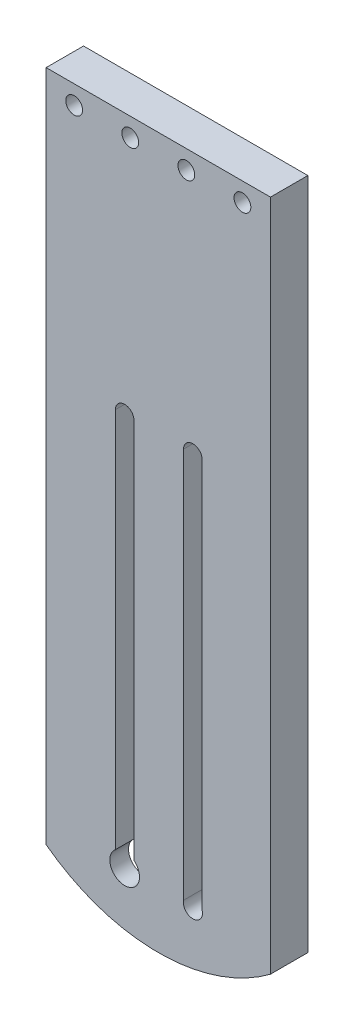
SolidWorks part; units mm, degrees
material "Сплав 2024"
ref_plane "Спереди" through (0, 0, 0) normal (0, 0, 1) x (1, 0, 0)
ref_plane "Сверху" through (0, 0, 0) normal (0, 1, 0) x (1, 0, 0)
ref_plane "Справа" through (0, 0, 0) normal (1, 0, 0) x (0, 0, -1)
sketch "Эскиз1" plane through (0, 0, 0) normal (0, 0, 1) x (1, 0, 0)
  line L0 (31.6276, -80) -> (0, -80) construction
  line L1 (0, 0) -> (60, 0)
  line L2 (0, 0) -> (0, -190)
  line L3 (0, -190) -> (60, -190)
  line L4 (60, 0) -> (60, -60)
  line L5 (30, 0) -> (30, -190) construction
  line L6 (0, -60) -> (-30, -70.9191) construction
  line L7 (-30, -70.9191) -> (-30, -139.0809) construction
  line L8 (-30, -139.0809) -> (0, -150) construction
  line L9 (0, 0) -> (0, -60) construction
  line L10 (0, -150) -> (0, -190) construction
  line L11 (60, -60) -> (60, -150)
  line L15 (60, -150) -> (60, -190)
  line L16 (90, -139.0809) -> (60, -150) construction
  line L17 (90, -70.9191) -> (90, -139.0809) construction
  line L18 (60, -60) -> (90, -70.9191) construction
  dimension "D1" = 40
  dimension "D2" = 190
  dimension "D3" = 80
  dimension "D4" = 60
  dimension "D5" = 60
  dimension "D6" = 90
  dimension "D7" = 110
  dimension "D8" = 110
extrude "Бобышка-Вытянуть1" add sketch "Эскиз1" along normal blind 10
sketch "Эскиз4" plane through (0, 0, 0) normal (0, 0, -1) x (-1, 0, 0)
  line L0 (-30, 0) -> (-30, -190) construction
  line L1 (-40.1, -15) -> (-19.9, -15)
  line L2 (-40.1, -15) -> (-40.1, -64.75)
  line L3 (-40.1, -64.75) -> (-19.9, -64.75)
  line L4 (-19.9, -15) -> (-19.9, -64.75)
  line L5 (-40.1, -15) -> (-19.9, -64.75) construction
  line L6 (-40.1, -64.75) -> (-19.9, -15) construction
  line L7 (0, 0) -> (-60, 0) construction
  point P0 (-30, -39.875)
  dimension "D1" = 20.2
  dimension "D2" = 15
  dimension "D4" = 49.75
hole_wizard "Цековка для винта с внутренним шестигранником M4" positions "Эскиз7" profile "Эскиз8" counterbore size "M4" standard "Ansi Metric"
sketch "Эскиз7" plane through (-14.8427, -41.6551, 0) normal (0, 0, -1) x (-1, 0, 0)
  point P0 (-67.3427, 36.6551)
  point P3 (-52.3427, 36.6551)
  point P6 (-37.3427, 36.6551)
  point P9 (-22.3427, 36.6551)
sketch "Эскиз8" plane through (52.5, -5, 0) normal (1, 0, 0) x (0, 1, 0)
  line L0 (0, 0) -> (0, 11.3509)
  line L1 (0, 11.3509) -> (2.25, 9.999)
  line L2 (2.25, 9.999) -> (2.25, 4)
  line L3 (2.25, 4) -> (4, 4)
  line L4 (4, 4) -> (4, 0)
  line L5 (4, 0) -> (0, 0)
  line L6 (0, 11.3509) -> (-2.25, 9.999) construction
  line L7 (0, -6.35) -> (0, 107.95) construction
  dimension "Диаметр отверстия" = 4.5
  dimension "Глубина отверстия" = 9.999
  dimension "Диаметр цековки" = 8
  dimension "Глубина цековки" = 4
  dimension "Угол заточки сверла" = 118
sketch "Эскиз9" plane through (0, 0, 10) normal (0, 0, -1) x (-1, 0, 0)
  line L0 (-39.25, -190) -> (-39.25, 0) construction
  line L1 (0, -190) -> (-60, -190) construction
  line L2 (-60, 0) -> (0, 0) construction
  line L3 (-21, -190) -> (-21, 0) construction
  line L4 (0, 0) -> (0, -190) construction
  line L5 (-60, -175) -> (0, -175) construction
  line L6 (-60, -190) -> (-60, 0) construction
  dimension "D1" = 18.25
  dimension "D2" = 21
  dimension "D3" = 15
hole_wizard "Отверстие обработанное метчиком 1/4-201" positions "Трехмерный эскиз1" profile "Эскиз10" tap size "1/4-20" standard "Ansi Inch" end condition through all
sketch3d "Трехмерный эскиз1"
  line L0 (60, -175, 10) -> (0, -175, 10) construction
  line L1 (39.25, -190, 10) -> (39.25, 0, 10) construction
  point P0 (39.25, -175, 10)
sketch "Эскиз10" plane through (39.25, -175, 10) normal (1, 0, 0) x (0, -1, 0)
  line L0 (0, 0) -> (0, 10)
  line L1 (0, 10) -> (2.5527, 10)
  line L2 (2.5527, 10) -> (2.5527, 0)
  line L5 (2.5527, 0) -> (0, 0)
  line L11 (0, -6.35) -> (0, 107.95) construction
  dimension "Диаметр резьбы" = 5.1054
  dimension "Глубина проходного сверла" = 10
hole_wizard "Отверстие обработанное метчиком 3/8-161" positions "Трехмерный эскиз2" profile "Эскиз11" tap size "3/8-16" standard "Ansi Inch" end condition through all
sketch3d "Трехмерный эскиз2"
  line L0 (21, -190, 10) -> (21, 0, 10) construction
  line L1 (60, -175, 10) -> (0, -175, 10) construction
  point P0 (21, -175, 10)
sketch "Эскиз11" plane through (21, -175, 10) normal (1, 0, 0) x (0, -1, 0)
  line L0 (0, 0) -> (0, 10)
  line L1 (0, 10) -> (3.9687, 10)
  line L2 (3.9687, 10) -> (3.9687, 0)
  line L5 (3.9687, 0) -> (0, 0)
  line L11 (0, -6.35) -> (0, 107.95) construction
  dimension "Диаметр резьбы" = 7.9375
  dimension "Глубина проходного сверла" = 10
sketch "Эскиз12" plane through (0, 0, 10) normal (0, 0, 1) x (1, 0, 0)
  line L0 (39.25, -175) -> (39.25, -70) construction
  line L1 (39.25, -190) -> (39.25, 0) construction
  line L2 (36.75, -175) -> (36.75, -70)
  line L3 (41.75, -175) -> (41.75, -70)
  line L4 (21, -175) -> (21, -70) construction
  line L5 (21, -190) -> (21, 0) construction
  line L6 (18.5, -175) -> (18.5, -70)
  line L7 (23.5, -175) -> (23.5, -70)
  line L8 (31.75, -175) -> (31.75, -70) construction
  line L9 (46.75, -175) -> (46.75, -70) construction
  line L10 (13.5, -175) -> (13.5, -70) construction
  line L11 (28.5, -175) -> (28.5, -70) construction
  arc A0 (36.75, -175) -> (41.75, -175) centre (39.25, -175) ccw
  arc A1 (41.75, -70) -> (36.75, -70) centre (39.25, -70) ccw
  arc A2 (18.5, -175) -> (23.5, -175) centre (21, -175) ccw
  arc A3 (23.5, -70) -> (18.5, -70) centre (21, -70) ccw
  arc A4 (46.75, -70) -> (31.75, -70) centre (39.25, -70) ccw construction
  arc A5 (31.75, -175) -> (46.75, -175) centre (39.25, -175) ccw construction
  arc A6 (28.5, -70) -> (13.5, -70) centre (21, -70) ccw construction
  arc A7 (13.5, -175) -> (28.5, -175) centre (21, -175) ccw construction
  point P5 (39.25, -122.5)
  point P10 (21, -122.5)
  dimension "D1" = 2.5
  dimension "D2" = 105
  dimension "D3" = 5
extrude "Вырез-Вытянуть1" cut sketch "Эскиз12" against normal through all
sketch "Эскиз14" plane through (0, 0, 0) normal (0, 0, -1) x (-1, 0, 0)
  line L0 (-30, 0) -> (-30, 4.7493) construction
  line L1 (-40.1, -15) -> (-19.9, -15)
  line L2 (-40.1, -15) -> (-40.1, -55)
  line L3 (-40.1, -55) -> (-19.9, -55)
  line L4 (-19.9, -15) -> (-19.9, -55)
  line L5 (-40.1, -15) -> (-19.9, -55) construction
  line L6 (-40.1, -55) -> (-19.9, -15) construction
  line L7 (-60, 0) -> (0, 0) construction
  point P0 (-30, -35)
  dimension "D1" = 20.2
  dimension "D2" = 40
  dimension "D3" = 15
sketch "Эскиз15" plane through (0, 0, 0) normal (0, 0, -1) x (-1, 0, 0)
  line L1 (-40.1, -55) -> (-19.9, -55) construction
  line L2 (-19.9, -15) -> (-19.9, -55) construction
  line L4 (-40.1, -15) -> (-40.1, -55) construction
  circle A0 centre (-39.1, -54) radius 2
  circle A1 centre (-20.9, -54) radius 2
  dimension "D1" = 4
  dimension "D2" = 4
  dimension "D3" = 1
  dimension "D4" = 1
  dimension "D5" = 1
  dimension "D6" = 1
extrude "Вырез-Вытянуть2" cut sketch "Эскиз14" against normal blind 7
extrude "Вырез-Вытянуть3" cut sketch "Эскиз15" against normal blind 7
sketch "Эскиз16" plane through (0, 0, 0) normal (0, 0, -1) x (-1, 0, 0)
  line L0 (0, -180) -> (0, -195)
  line L1 (-60, -195) -> (0, -195)
  line L2 (-60, -195) -> (-60, -180)
  line L3 (0, -190) -> (-60, -190) construction
  line L4 (-30, 0) -> (-30, -190) construction
  line L5 (0, 0) -> (-60, 0) construction
  arc A0 (0, -180) -> (-60, -180) centre (-30, -140) cw
  dimension "D1" = 5
  dimension "D3" = 140
extrude "Вырез-Вытянуть4" cut sketch "Эскиз16" against normal through all
sketch "Эскиз19" plane through (0, 0, 0) normal (0, 0, -1) x (-1, 0, 0)
  line L1 (-60, -60) -> (-60, -150) construction
  line L2 (-57, -61) -> (-53, -61) construction
  line L3 (-57, -61) -> (-57, -177.4166)
  line L4 (-57, -177.4166) -> (-53, -177.4166) construction
  line L5 (-53, -61) -> (-53, -177.4166)
  line L7 (-60, -59) -> (0, -59) construction
  line L8 (-60, 0) -> (-60, -60) construction
  line L9 (0, 0) -> (0, -190) construction
  line L10 (-37.3679, -55) -> (-22.6321, -55) construction
  line L11 (-30, 0) -> (-30, -6.6536) construction
  line L12 (-30, 0) -> (-30, -190) construction
  line L13 (-3, -177.4166) -> (-7, -177.4166) construction
  line L14 (-3, -61) -> (-7, -61) construction
  line L15 (-7, -61) -> (-7, -177.4166)
  line L16 (-3, -61) -> (-3, -177.4166)
  arc A0 (-53, -61) -> (-57, -61) centre (-55, -61) ccw
  arc A1 (-57, -177.4166) -> (-53, -177.4166) centre (-55, -177.4166) ccw
  arc A4 (-3, -177.4166) -> (-7, -177.4166) centre (-5, -177.4166) cw
  arc A5 (-58.2, -177.6) -> (-1.8, -177.6) centre (-30, -140) ccw
  arc A6 (-58.2, -177.6) -> (-1.8, -177.6) centre (-30, -140) ccw construction
  arc A7 (-7, -61) -> (-3, -61) centre (-5, -61) cw
  dimension "D1" = 4
  dimension "D3" = 3
  dimension "D2" = 3
  dimension "D4" = 4
extrude "Вырез-Вытянуть7" cut sketch "Эскиз19" against normal blind 5
sketch "Эскиз20" plane through (0, 0, 0) normal (0, 0, -1) x (-1, 0, 0)
  line L0 (-50, -59) -> (-50, -182.5323)
  line L1 (-10, -182.5323) -> (-10, -59)
  line L2 (-10, -59) -> (-50, -59)
  line L3 (-53, -177.4166) -> (-53, -61) construction
  line L4 (-7, -61) -> (-7, -177.4166) construction
  line L5 (-37.3679, -55) -> (-22.6321, -55) construction
  arc A2 (-58.2, -177.6) -> (-1.8, -177.6) centre (-30, -140) ccw
  arc A3 (-50, -182.5323) -> (-10, -182.5323) centre (-30, -140) ccw
  dimension "D2" = 3
  dimension "D3" = 3
  dimension "D4" = 4
  dimension "D1" = 3
extrude "Вырез-Вытянуть8" cut sketch "Эскиз20" against normal blind 5
sketch "Эскиз18" plane through (0, 0, 0) normal (0, 0, -1) x (-1, 0, 0)
  line L0 (-60, 0) -> (-60, -60) construction
  line L1 (-57, -15) -> (-44.1, -15)
  line L2 (-57, -15) -> (-57, -55)
  line L3 (-57, -55) -> (-44.1, -55)
  line L4 (-44.1, -15) -> (-44.1, -55)
  line L6 (-40.1, -15) -> (-40.1, -52.2679) construction
  line L8 (-30, 0) -> (-30, -5.8743) construction
  line L9 (-30, 0) -> (-30, -190) construction
  line L10 (-15.9, -15) -> (-15.9, -55)
  line L11 (-3, -55) -> (-15.9, -55)
  line L12 (-3, -15) -> (-3, -55)
  line L13 (-3, -15) -> (-15.9, -15)
  line L14 (-37.3679, -55) -> (-22.6321, -55) construction
  line L15 (-19.9, -15) -> (-40.1, -15) construction
  point P6 (-40.1, -33.634)
  dimension "D1" = 3
  dimension "D3" = 4
extrude "Вырез-Вытянуть6" cut sketch "Эскиз18" against normal blind 5
fillet "Скругление1" radius 3 18 edges at (3, -15, 2.5) (15.9, -15, 2.5) (3, -55, 2.5) (15.9, -55, 2.5) (19.9, -52.2679, 3.5) (22.6321, -55, 3.5) (37.3679, -55, 3.5) (40.1, -52.2679, 3.5) (19.9, -15, 3.5) (40.1, -15, 3.5) (44.1, -55, 2.5) (57, -55, 2.5) (44.1, -15, 2.5) (57, -15, 2.5) (10, -182.5323, 2.5) (50, -182.5323, 2.5) (10, -59, 2.5) (50, -59, 2.5)
equation "\"D6@Эскиз1\"=\"D5@Эскиз1\"+30"
equation "\"D2@Эскиз15\" = \"D1@Эскиз15\""
